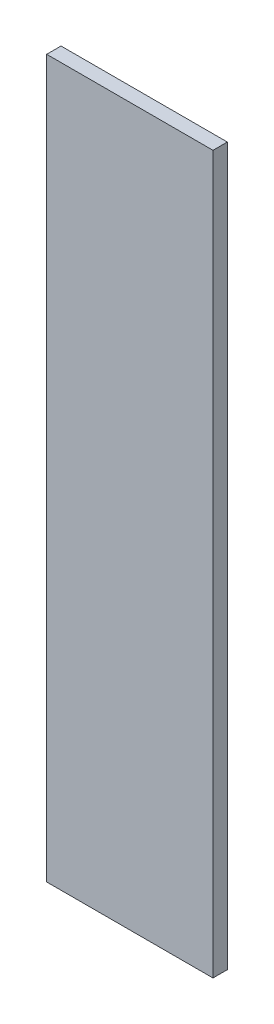
SolidWorks part; units mm, degrees
ref_plane "Plan de face" through (0, 0, 0) normal (0, 0, 1) x (1, 0, 0)
ref_plane "Plan de dessus" through (0, 0, 0) normal (0, 1, 0) x (1, 0, 0)
ref_plane "Plan de droite" through (0, 0, 0) normal (1, 0, 0) x (0, 0, -1)
sketch "Esquisse1" plane through (0, 0, 0) normal (0, 0, 1) x (1, 0, 0)
  line L0 (0, 0) -> (58, 0)
  line L1 (58, 0) -> (58, 250)
  line L2 (58, 250) -> (0, 250)
  line L3 (0, 250) -> (0, 0)
extrude "Boss.-Extru.1" add sketch "Esquisse1" along normal blind 5
